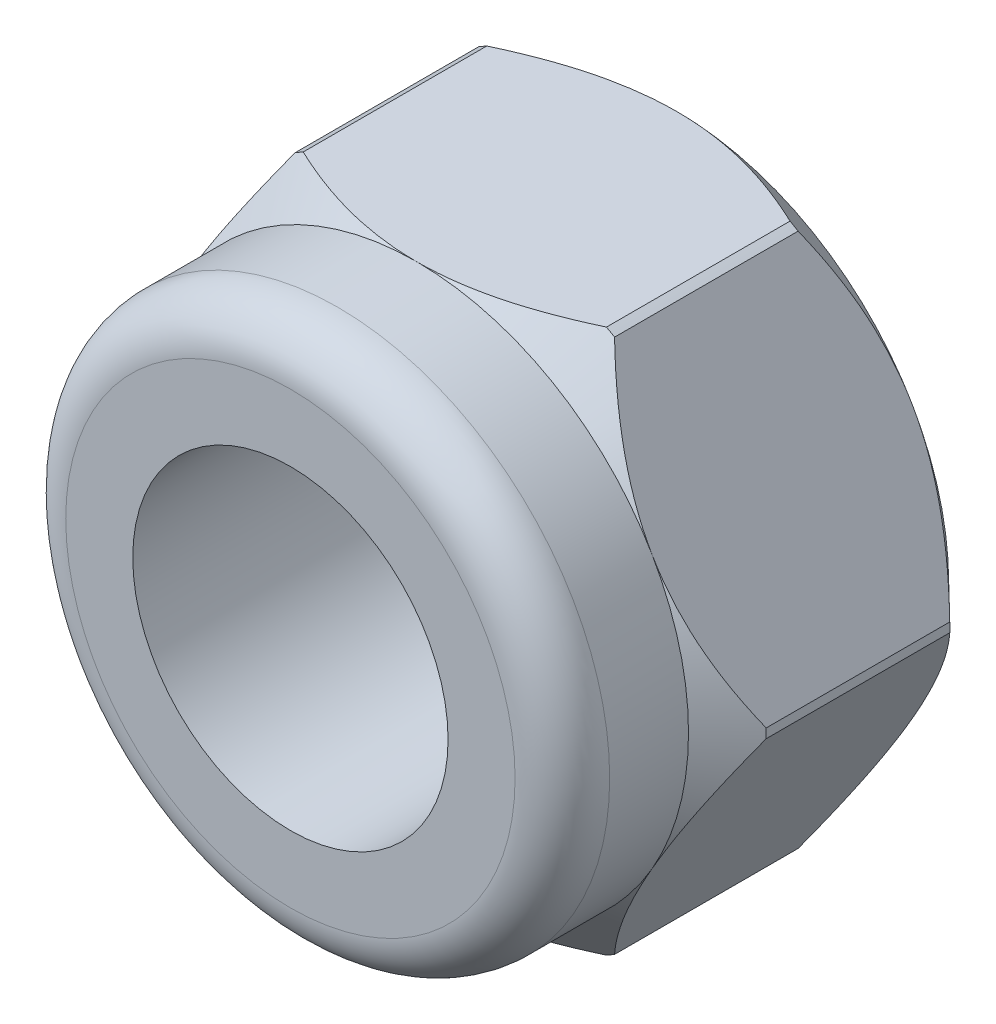
SolidWorks part; units mm, degrees
ref_plane "Front Plane" through (0, 0, 0) normal (0, 0, 1) x (1, 0, 0)
ref_plane "Top Plane" through (0, 0, 0) normal (0, 1, 0) x (1, 0, 0)
ref_plane "Right Plane" through (0, 0, 0) normal (1, 0, 0) x (0, 0, -1)
sketch "Sketch1" plane through (0, 0, 0) normal (0, 0, 1) x (1, 0, 0)
  line L0 (0, 3.9837) -> (0, 0) construction
  line L1 (0, 0) -> (3.9837, 0) construction
  line L2 (-1.9919, 3.45) -> (1.9919, 3.45)
  line L3 (1.9919, 3.45) -> (3.9837, 0)
  line L4 (1.9919, -3.45) -> (3.9837, 0)
  line L5 (-1.9919, -3.45) -> (1.9919, -3.45)
  line L6 (-1.9919, 3.45) -> (-3.9837, 0)
  line L7 (-1.9919, -3.45) -> (-3.9837, 0)
  circle A0 centre (0, 0) radius 3.9837 construction
  circle A1 centre (0, 0) radius 3.45 construction
  circle A2 centre (0, 0) radius 2
  point P12 (0, 3.45)
  point P14 (0, -3.45)
  dimension "D1" = 6.9
  dimension "D2" = 4
extrude "Boss-Extrude1" add sketch "Sketch1" along normal blind 3.3
sketch "Sketch2" plane through (0, 0, 3.3) normal (0, 0, 1) x (1, 0, 0)
  line L0 (-1.9919, 3.45) -> (-3.9837, 0) construction
  circle A0 centre (0, 0) radius 3.45
  circle A1 centre (0, 0) radius 2 construction
  circle A2 centre (0, 0) radius 2
extrude "Boss-Extrude2" add sketch "Sketch2" along normal blind 1.6
fillet "Fillet1" radius 0.6 1 edges at (3.45, 0, 4.9)
sketch "Sketch3" plane through (0, 0, 0) normal (1, 0, 0) x (0, 0, -1)
  line L0 (-3.3, 3.45) -> (-2.8143, 3.95)
  line L1 (-2.8143, 3.95) -> (-0.4857, 3.95)
  line L2 (-0.4857, 3.95) -> (0, 3.45)
  line L3 (0, 3.45) -> (0, 4.7193)
  line L4 (0, 4.7193) -> (-3.3, 4.7193)
  line L5 (-3.3, 4.7193) -> (-3.3, 3.45)
  line L6 (-3.3, 3.45) -> (0, 3.45) construction
  line L8 (0, 0) -> (1.9305, 0) construction
  point P9 (-1.65, 4.7193)
  point P12 (-0.4857, 3.95)
  point P14 (-1.65, 3.95)
  dimension "D1" = 0.5
revolve "Cut-Revolve1" cut sketch "Sketch3" angle 360 about L8
chamfer "Chamfer1" distance 0.3 angle 45 1 edges at (2, 0, 0)
